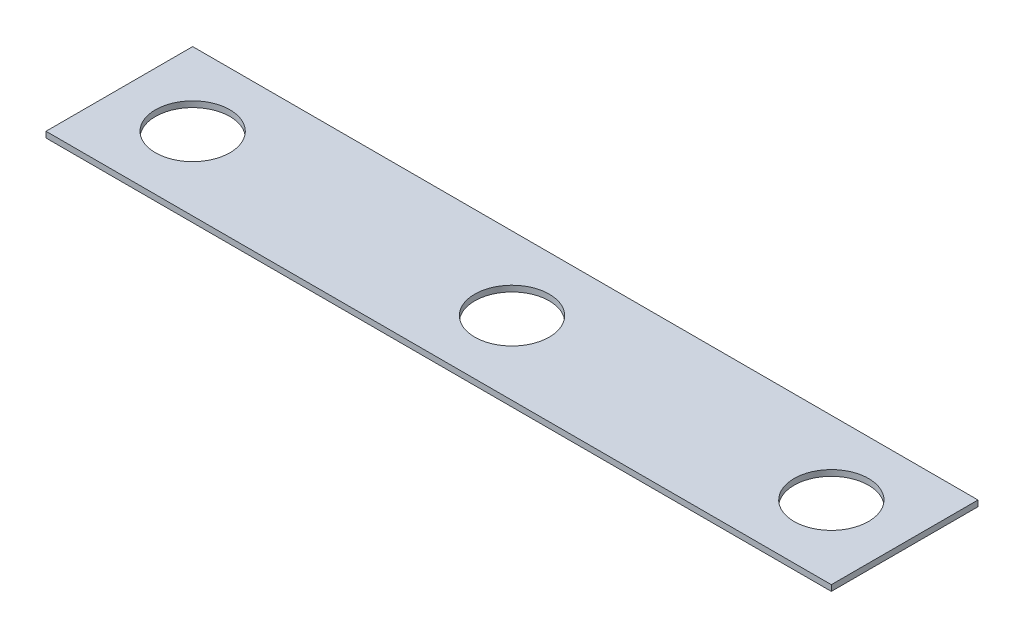
SolidWorks part; units mm, degrees
ref_plane "Front Plane" through (0, 0, 0) normal (0, 0, 1) x (1, 0, 0)
ref_plane "Top Plane" through (0, 0, 0) normal (0, 1, 0) x (1, 0, 0)
ref_plane "Right Plane" through (0, 0, 0) normal (1, 0, 0) x (0, 0, -1)
sketch "Sketch1" plane through (0, 0, 0) normal (0, 1, 0) x (1, 0, 0)
  line L1 (-8.5, -1.5875) -> (8.5, -1.5875)
  line L2 (-8.5, -1.5875) -> (-8.5, 1.5875)
  line L3 (-8.5, 1.5875) -> (8.5, 1.5875)
  line L4 (8.5, -1.5875) -> (8.5, 1.5875)
  line L5 (-8.5, -1.5875) -> (8.5, 1.5875) construction
  line L6 (-8.5, 1.5875) -> (8.5, -1.5875) construction
  point P0 (0, 0)
  dimension "D1" = 3.175
  dimension "D2" = 17
extrude "Boss-Extrude1" add sketch "Sketch1" along normal blind 0.127
hole_wizard "#0 Clearance Hole1" positions "Sketch3" profile "Sketch2" hole size "#0" standard "Ansi Inch"
sketch "Sketch3" plane through (0, 0.127, 0) normal (0, 1, 0) x (-1, 0, 0)
  line L0 (8.5, -1.5875) -> (8.5, 1.5875) construction
  line L1 (-8.5, 1.5875) -> (-8.5, -1.5875) construction
  point P1 (0, 0)
  point P4 (-6.9125, 0)
  point P6 (6.9125, 0)
  dimension "D1" = 1.5875
  dimension "D2" = 1.5875
sketch "Sketch2" plane through (0, 0.127, 0) normal (1, 0, 0) x (0, 0, 1)
  line L0 (0, 0) -> (0, 5.3106)
  line L1 (0, 5.3106) -> (0.8064, 4.826)
  line L2 (0.8064, 4.826) -> (0.8064, 0)
  line L5 (0.8064, 0) -> (0, 0)
  line L10 (0, 5.3106) -> (-0.8065, 4.826) construction
  line L11 (0, -6.35) -> (0, 107.95) construction
  dimension "Hole Dia." = 1.6129
  dimension "Hole Depth" = 4.826
  dimension "Drill Angle" = 118
